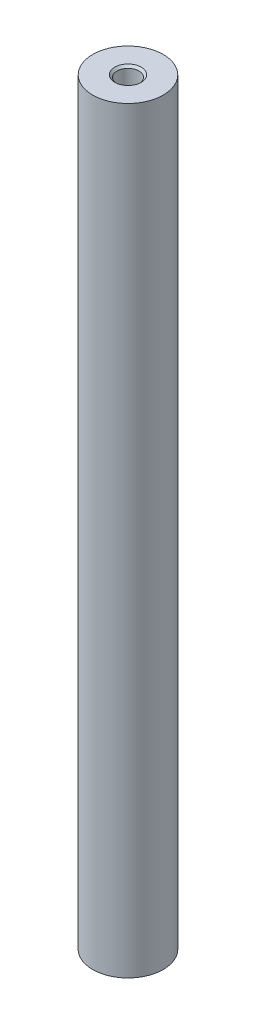
SolidWorks part; units mm, degrees
material "AISI 316 Stainless Steel Sheet (SS)"
ref_plane "Front Plane" through (0, 0, 0) normal (0, 0, 1) x (1, 0, 0)
ref_plane "Top Plane" through (0, 0, 0) normal (0, 1, 0) x (1, 0, 0)
ref_plane "Right Plane" through (0, 0, 0) normal (1, 0, 0) x (0, 0, -1)
sketch "Sketch1" plane through (0, 0, 0) normal (0, 1, 0) x (1, 0, 0)
  circle A0 centre (0, 0) radius 8
  dimension "D1" = 16
extrude "Boss-Extrude1" add sketch "Sketch1" along normal blind 172
sketch "Sketch2" plane through (0, 0, 0) normal (0, -1, 0) x (1, 0, 0)
  circle A0 centre (0, 0) radius 2.5
  dimension "D1" = 5
extrude "Cut-Extrude1" cut sketch "Sketch2" against normal blind 15
ref_plane "Plane1" through (0, 86, 0) normal (0, 1, 0) x (1, 0, 0)
mirror "Mirror1" about plane through (0, 86, 0) normal (0, 1, 0) of "Cut-Extrude1"
chamfer "Chamfer1" distance 0.5 angle 45 2 edges at (0, 0, -2.5) (0, 172, -2.5)
